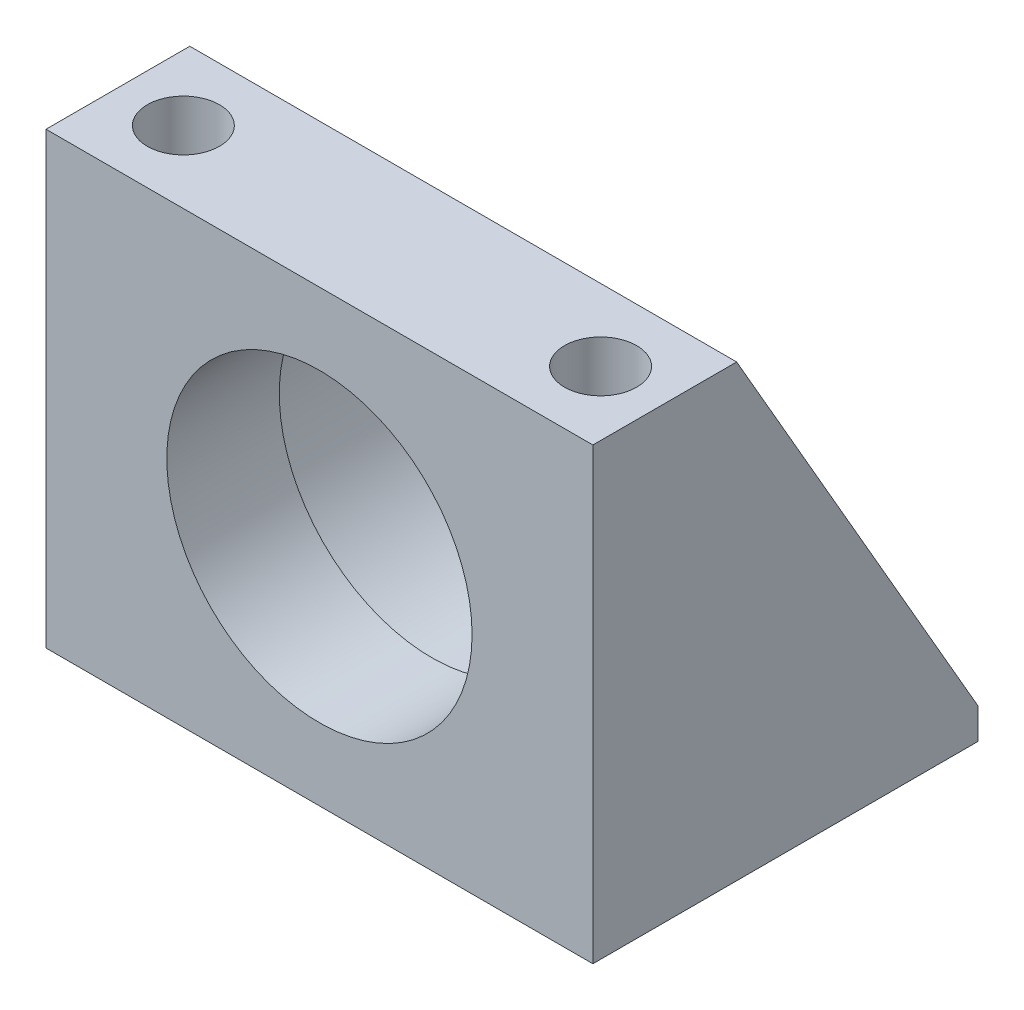
SolidWorks part; units mm, degrees
material "Alloy Steel"
ref_plane "Front Plane" through (0, 0, 0) normal (0, 0, 1) x (1, 0, 0)
ref_plane "Top Plane" through (0, 0, 0) normal (0, 1, 0) x (1, 0, 0)
ref_plane "Right Plane" through (0, 0, 0) normal (1, 0, 0) x (0, 0, -1)
sketch "Sketch1" plane through (0, 0, 0) normal (0, 0, 1) x (1, 0, 0)
  line L1 (-27.051, 44.45) -> (27.051, 44.45)
  line L2 (-27.051, 44.45) -> (-27.051, 0)
  line L3 (-27.051, 0) -> (27.051, 0)
  line L4 (27.051, 44.45) -> (27.051, 0)
  circle A0 centre (0, 22.225) radius 15.1003
  dimension "D4" = 30.2006
  dimension "D1" = 54.102
  dimension "D2" = 44.45
  dimension "D3" = 22.225
extrude "Extrude1" add sketch "Sketch1" against normal blind 38.1
sketch "Sketch2" plane through (27.051, 0, 0) normal (1, 0, 0) x (0, 0, -1)
  line L0 (14.224, 44.45) -> (38.1, 3.048)
  line L1 (0, 0) -> (0, 44.45) construction
  line L2 (38.1, 0) -> (0, 0) construction
  line L4 (0, 44.45) -> (0, 0)
  line L5 (0, 0) -> (38.1, 0)
  line L6 (38.1, 0) -> (38.1, 44.45)
  line L7 (38.1, 44.45) -> (0, 44.45)
  line L10 (38.1, 3.048) -> (38.1, 44.45)
  line L11 (38.1, 44.45) -> (14.224, 44.45)
  dimension "D2" = 14.224
  dimension "D3" = 3.048
  dimension "D1" = 0
extrude "Cut-Extrude1" cut sketch "Sketch2" against normal through all
sketch "Sketch3" plane through (0, 0, -38.1) normal (0, 0, -1) x (-1, 0, 0)
  circle A0 centre (0, 22.225) radius 17.526
  dimension "D1" = 35.052
extrude "Cut-Extrude2" cut sketch "Sketch3" against normal offset from surface (26.9748 mm away) 11.1252 up to face at (15.1003, 22.225, 0)
fillet "Fillet1" radius 1.524 1 edges at (17.526, 22.225, -11.1252)
hole_wizard "Hole1" positions "Sketch5" profile "Sketch4" legacy end condition up to next
sketch "Sketch5" plane through (0, 44.45, 0) normal (0, 1, 0) x (-1, 0, 0)
  line L0 (-27.051, -14.224) -> (-27.051, 0) construction
  line L1 (-27.051, 0) -> (27.051, 0) construction
  point P0 (20.574, -7.112)
  point P1 (-20.701, -7.112)
  dimension "D1" = 6.35
  dimension "D2" = 7.112
  dimension "D3" = 41.275
sketch "Sketch4" plane through (-20.574, 44.45, -7.112) normal (1, 0, 0) x (0, 0, 1)
  line L0 (0, 0) -> (0, 44.45)
  line L1 (0, 44.45) -> (3.5687, 44.45)
  line L2 (3.5687, 44.45) -> (3.5687, 0)
  line L3 (3.5687, 0) -> (0, 0)
  line L4 (0, 110) -> (0, -10) construction
  dimension "Diameter" = 7.1374
  dimension "Depth" = 44.45
